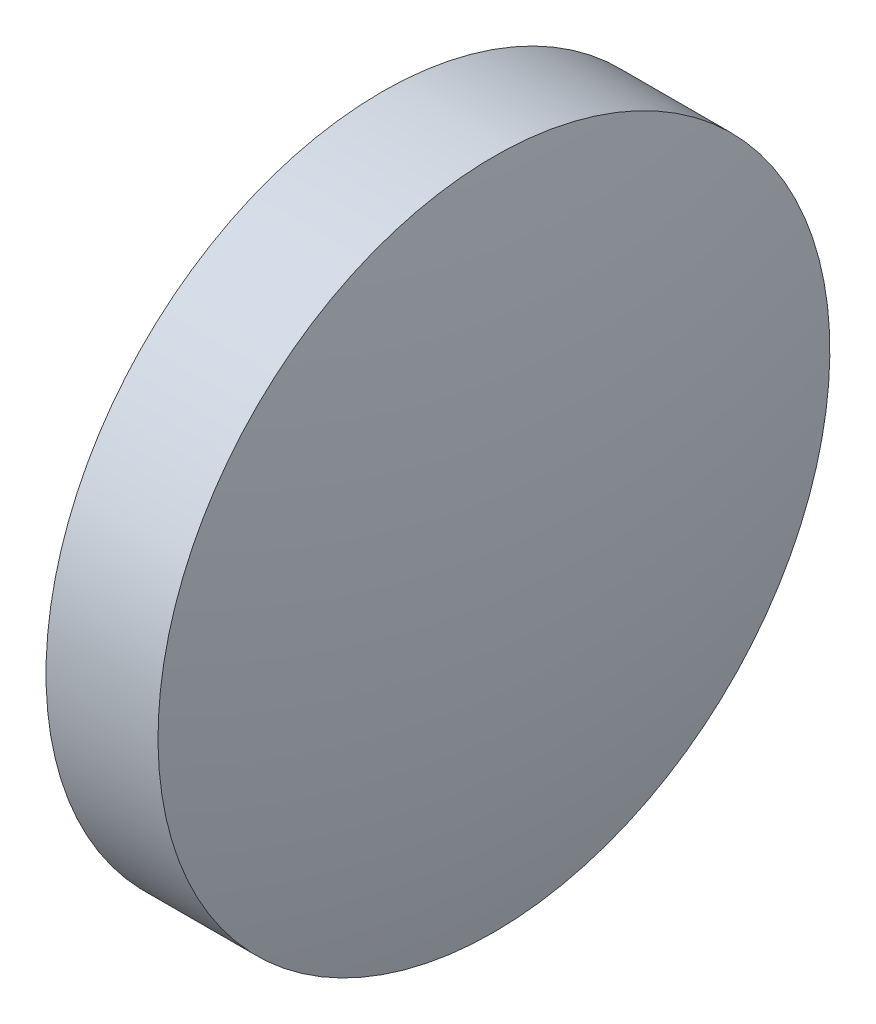
SolidWorks part; units mm, degrees
ref_plane "前视基准面" through (0, 0, 0) normal (0, 0, 1) x (1, 0, 0)
ref_plane "上视基准面" through (0, 0, 0) normal (0, 1, 0) x (1, 0, 0)
ref_plane "右视基准面" through (0, 0, 0) normal (1, 0, 0) x (0, 0, -1)
sketch "草图1" plane through (0, 0, 0) normal (0, 0, 1) x (1, 0, 0)
  line L0 (19.9232, 14.4841) -> (20.9232, 14.4841)
  line L1 (20.9232, 14.4841) -> (20.9232, 8.4841)
  line L2 (20.9232, 8.4841) -> (19.9232, 8.4841)
  line L3 (19.9232, 8.4841) -> (19.9232, 14.4841)
  line L4 (19.3224, 11.4841) -> (21.5079, 11.4841) construction
  arc A0 (19.9232, 14.4841) -> (19.9232, 8.4841) centre (34.0516, 11.4841) ccw
  arc A1 (20.9232, 8.4841) -> (20.9232, 14.4841) centre (6.7948, 11.4841) ccw
  dimension "D1" = 6
  dimension "D2" = 1
revolve "旋转1" add sketch "草图1" angle 360 about L4
